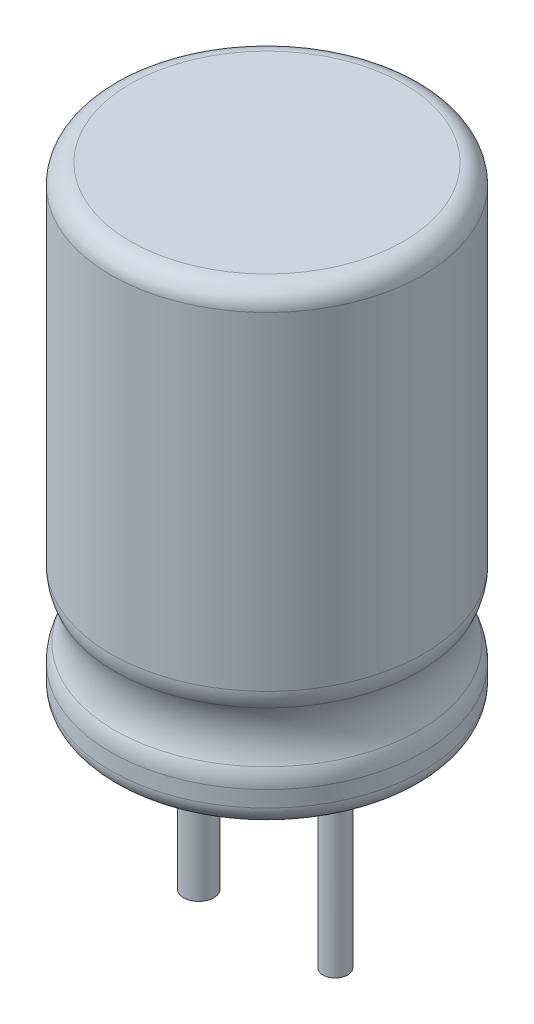
SolidWorks part; units mm, degrees
ref_plane "Front Plane" through (0, 0, 0) normal (0, 0, 1) x (1, 0, 0)
ref_plane "Top Plane" through (0, 0, 0) normal (0, 1, 0) x (1, 0, 0)
ref_plane "Right Plane" through (0, 0, 0) normal (1, 0, 0) x (0, 0, -1)
sketch "Sketch1" plane through (0, 0, 0) normal (0, 1, 0) x (1, 0, 0)
  circle A0 centre (0, 0) radius 4
  dimension "D1" = 8
extrude "Boss-Extrude1" add sketch "Sketch1" along normal blind 12
sketch "Sketch2" plane through (0, 0, 0) normal (0, -1, 0) x (1, 0, 0)
  line L0 (-6.4573, 0) -> (7.0651, 0) construction
  circle A0 centre (1.75, 0) radius 0.3176
  circle A1 centre (-1.75, 0) radius 0.3885
  dimension "D1" = 3.5
  dimension "D2" = 1.75
extrude "Boss-Extrude2" add sketch "Sketch2" along normal blind 5
ref_axis "Axis1" through (0, 22.7815, 0) along (0, -1, 0)
sketch "Sketch3" plane through (0, 0, 0) normal (1, 0, 0) x (0, 0, -1)
  line L0 (-9.0697, 2) -> (9.3527, 2) construction
  circle A0 centre (5.25, 2) radius 1.5
  dimension "D3" = 3
  dimension "D1" = 2
  dimension "D2" = 5.25
revolve "Cut-Revolve1" cut sketch "Sketch3" angle 360 about axis through (0, 22.7815, 0) along (0, -1, 0)
fillet "Fillet1" radius 1 2 edges at (0, 1.1708, 4) (0, 2.8292, -4)
fillet "Fillet2" radius 0.5 1 edges at (0, 12, 4)
fillet "Fillet3" radius 0.5 1 edges at (0, 0, 4)
